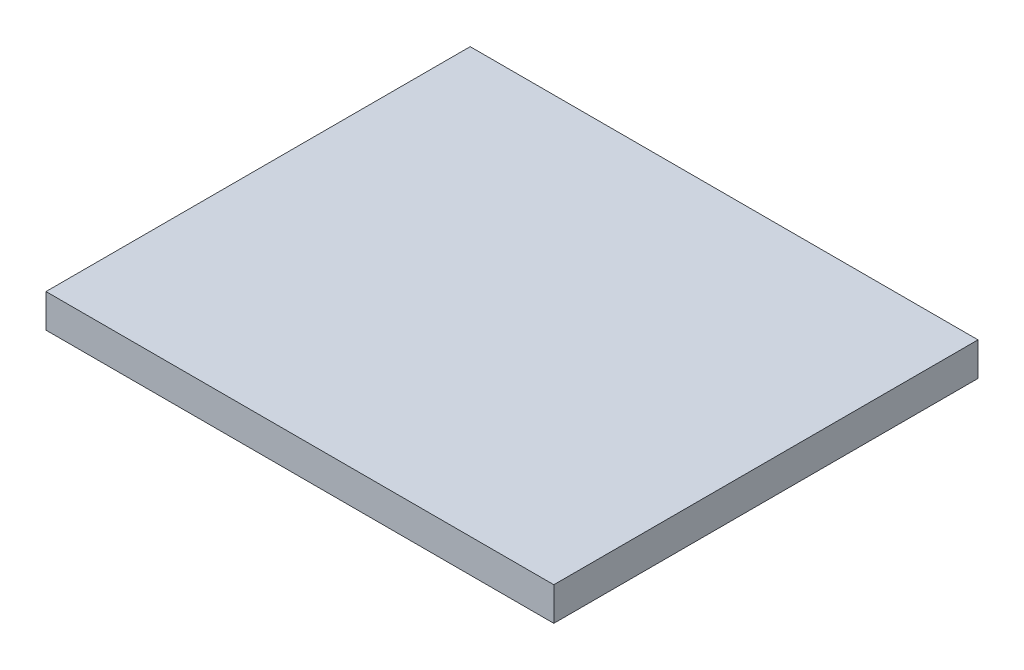
SolidWorks part; units mm, degrees
material "metal_resistor"
ref_plane "Front Plane" through (0, 0, 0) normal (0, 0, 1) x (1, 0, 0)
ref_plane "Top Plane" through (0, 0, 0) normal (0, 1, 0) x (1, 0, 0)
ref_plane "Right Plane" through (0, 0, 0) normal (1, 0, 0) x (0, 0, -1)
sketch "Sketch2" plane through (0, 0, 0) normal (0, 1, 0) x (1, 0, 0)
  line L0 (-10.1409, 2.6416) -> (-1.6409, 2.6416)
  line L1 (-10.1409, 2.6416) -> (-10.1409, -4.4584)
  line L2 (-10.1409, -4.4584) -> (-1.6409, -4.4584)
  line L3 (-1.6409, 2.6416) -> (-1.6409, -4.4584)
extrude "Boss-Extrude1" add sketch "Sketch2" along normal blind 0.56
